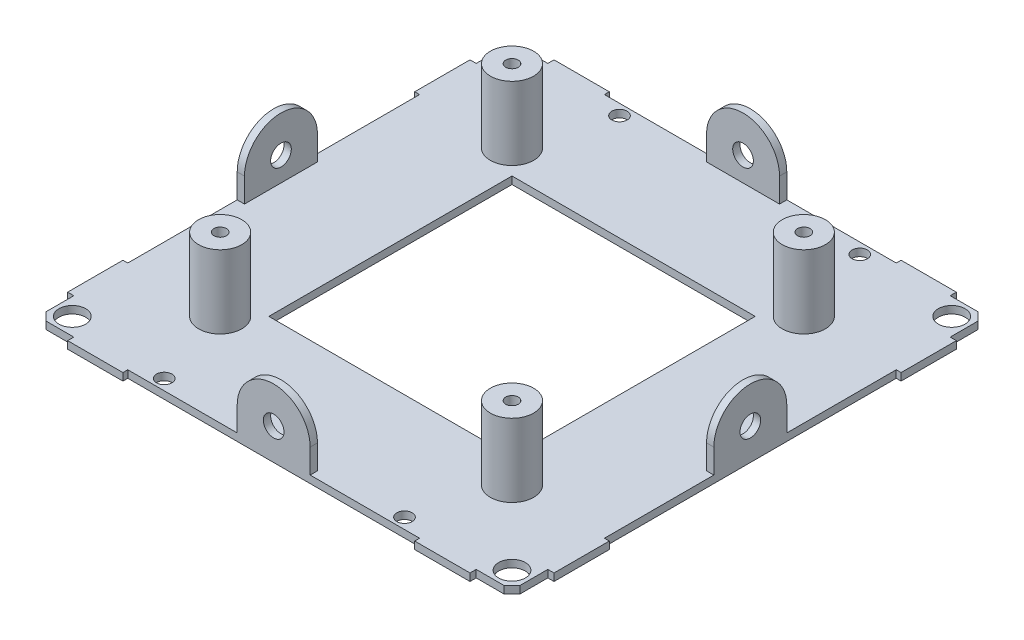
SolidWorks part; units mm, degrees
material "5052-H38"
ref_plane "Front Plane" through (0, 0, 0) normal (0, 0, 1) x (1, 0, 0)
ref_plane "Top Plane" through (0, 0, 0) normal (0, 1, 0) x (1, 0, 0)
ref_plane "Right Plane" through (0, 0, 0) normal (1, 0, 0) x (0, 0, -1)
sketch "Sketch1" plane through (0, 0, 0) normal (0, 1, 0) x (1, 0, 0)
  line L0 (-50, 50) -> (-41.364, 50)
  line L1 (-50, -50) -> (50, -50)
  line L2 (-50, -50) -> (-50, 50)
  line L3 (-50, 50) -> (50, 50)
  line L4 (50, -50) -> (50, 50)
  line L5 (-50, -50) -> (50, 50) construction
  line L6 (-50, 50) -> (50, -50) construction
  line L7 (-50, 50) -> (-50, 41.364)
  line L8 (-50, 41.364) -> (-48.73, 41.364)
  line L9 (-48.73, 41.364) -> (-48.73, 47.079)
  line L10 (-41.364, 50) -> (-41.364, 48.73)
  line L11 (-41.364, 48.73) -> (-47.079, 48.73)
  line L12 (-47.079, 48.73) -> (-48.73, 47.079)
  line L13 (-50, 50) -> (-45.2, 50) construction
  line L14 (-45.2, 50) -> (-45.2, 45.2) construction
  line L15 (50, 50) -> (50, 41.364)
  line L16 (50, 41.364) -> (48.73, 41.364)
  line L17 (48.73, 41.364) -> (48.73, 47.079)
  line L18 (48.73, 47.079) -> (47.079, 48.73)
  line L19 (41.364, 48.73) -> (47.079, 48.73)
  line L20 (41.364, 50) -> (41.364, 48.73)
  line L21 (50, 50) -> (41.364, 50)
  line L22 (50, -50) -> (41.364, -50)
  line L23 (41.364, -50) -> (41.364, -48.73)
  line L24 (41.364, -48.73) -> (47.079, -48.73)
  line L25 (47.079, -48.73) -> (48.73, -47.079)
  line L26 (48.73, -41.364) -> (48.73, -47.079)
  line L27 (50, -41.364) -> (48.73, -41.364)
  line L28 (50, -50) -> (50, -41.364)
  line L29 (-50, -50) -> (-50, -41.364)
  line L30 (-50, -41.364) -> (-48.73, -41.364)
  line L31 (-48.73, -41.364) -> (-48.73, -47.079)
  line L32 (-48.73, -47.079) -> (-47.079, -48.73)
  line L33 (-41.364, -48.73) -> (-47.079, -48.73)
  line L34 (-41.364, -50) -> (-41.364, -48.73)
  line L35 (-50, -50) -> (-41.364, -50)
  line L36 (0, -50) -> (0, 50) construction
  line L37 (-1000, 46.8) -> (49000, 46.8) construction
  line L38 (24.7, 46.8) -> (-24.7, 46.8)
  line L39 (-1000, 0) -> (49000, 0) construction
  line L41 (-25, -25) -> (25, -25)
  line L42 (-25, -25) -> (-25, 25)
  line L43 (-25, 25) -> (25, 25)
  line L44 (25, -25) -> (25, 25)
  line L45 (-25, -25) -> (25, 25) construction
  line L46 (-25, 25) -> (25, -25) construction
  circle A0 centre (-45.2, 45.2) radius 2.7503
  circle A1 centre (45.2, 45.2) radius 2.7503
  circle A2 centre (45.2, -45.2) radius 2.7503
  circle A3 centre (-45.2, -45.2) radius 2.7503
  circle A4 centre (-24.7, 46.8) radius 1.575
  circle A5 centre (24.7, 46.8) radius 1.575
  circle A6 centre (24.7, -46.8) radius 1.575
  circle A7 centre (-24.7, -46.8) radius 1.575
  point P0 (0, 0)
  point P15 (0, 46.8)
  point P45 (0, 0)
  point P46 (0, 0)
  point P48 (-24.7, 46.8)
  point P53 (0, 46.8)
  point P61 (25, 25)
  point P63 (0, 0)
  dimension "D4" = 4
  dimension "D1" = 100
  dimension "D2" = 100
  dimension "D3" = 8.636
  dimension "D5" = 3.2
  dimension "D6" = 24.7
extrude "Boss-Extrude1" add sketch "Sketch1" along normal blind 1.524 contours L37 A5 L38 A4 A0 L9 L8 L2 L30 L31 L32 L33 L34 L1 L23 L24 L25 L26 L27 L4 L16 L17 A1 A2 A3 A6 A7
sketch "Sketch2" plane through (0, 1.524, 0) normal (0, 1, 0) x (1, 0, 0)
  line L0 (0, -1000) -> (0, 49000) construction
  line L1 (0, 50) -> (0, 45) construction
  line L2 (-41.364, 50) -> (41.364, 50) construction
  line L3 (-7.5, 47.5) -> (7.5, 47.5) construction
  line L4 (-7.5, 47.5) -> (7.5, 47.5)
  line L5 (-7.5, 47.5) -> (-7.5, 50)
  line L6 (7.5, 47.5) -> (7.5, 50)
  line L7 (-7.5, 50) -> (7.5, 50)
  line L8 (47.5, 7.5) -> (47.5, -7.5)
  line L9 (47.5, 7.5) -> (50, 7.5)
  line L10 (50, 7.5) -> (50, -7.5)
  line L11 (47.5, -7.5) -> (50, -7.5)
  line L12 (7.5, -47.5) -> (-7.5, -47.5)
  line L13 (7.5, -47.5) -> (7.5, -50)
  line L14 (7.5, -50) -> (-7.5, -50)
  line L15 (-7.5, -47.5) -> (-7.5, -50)
  line L16 (-47.5, -7.5) -> (-47.5, 7.5)
  line L17 (-47.5, -7.5) -> (-50, -7.5)
  line L18 (-50, -7.5) -> (-50, 7.5)
  line L19 (-47.5, 7.5) -> (-50, 7.5)
  point P10 (0, 47.5)
  point P27 (0, 0)
  dimension "D1" = 15
  dimension "D2" = 4
extrude "Boss-Extrude2" add sketch "Sketch2" along normal blind 12.476 contours L4 L5 L7 L6 | L8 L11 L10 L9 | L12 L15 L14 L13 | L16 L19 L18 L17
sketch "Sketch3" plane through (0, 0, 50) normal (0, 0, 1) x (1, 0, 0)
  line L0 (-1007.5, 1.524) -> (48992.5, 1.524) construction
  line L1 (7.5, 1.524) -> (-7.5, 1.524) construction
  line L2 (-7.5, 14) -> (-7.5, 1.524) construction
  line L3 (0, 1.524) -> (0, 6.5) construction
  line L4 (7.5, 14) -> (7.5, 1.524) construction
  line L5 (7.5, 6.5) -> (7.5, 14)
  line L6 (7.5, 14) -> (-7.5, 14)
  line L7 (-7.5, 14) -> (-7.5, 6.5)
  circle A0 centre (0, 6.5) radius 2.125
  arc A1 (-7.5, 6.5) -> (7.5, 6.5) centre (0, 6.5) cw
  line M4 (7.5, 1.524) -> (7.5, 14)
  line M5 (7.5, 14) -> (-7.5, 14)
  line M6 (-7.5, 14) -> (-7.5, 1.524)
extrude "Cut-Extrude1" cut sketch "Sketch3" against normal through all both and the other way through all contours A1 M5 M4 | A1 L6 M6 | A0
sketch "Sketch4" plane through (-50, 0, 0) normal (-1, 0, 0) x (0, 0, 1)
  line L0 (-992.5, 1.524) -> (49007.5, 1.524) construction
  line L1 (-7.5, 1.524) -> (7.5, 1.524) construction
  line L2 (41.364, 1.524) -> (7.5, 1.524) construction
  line L3 (0, 1.524) -> (0, 6.5) construction
  line L4 (7.5, 14) -> (7.5, 1.524) construction
  line L5 (-7.5, 14) -> (-7.5, 1.524) construction
  line L6 (7.5, 6.5) -> (7.5, 14)
  line L7 (7.5, 14) -> (-7.5, 14)
  line L8 (-7.5, 14) -> (-7.5, 6.5)
  circle A0 centre (0, 6.5) radius 2.125
  arc A1 (7.5, 6.5) -> (-7.5, 6.5) centre (0, 6.5) ccw
  line M4 (7.5, 1.524) -> (7.5, 14)
  line M5 (7.5, 14) -> (-7.5, 14)
  line M6 (-7.5, 14) -> (-7.5, 1.524)
extrude "Cut-Extrude2" cut sketch "Sketch4" against normal through all both and the other way through all contours A0 | A1 M4 M5 | A1 L7 M6
sketch "Sketch5" plane through (0, 0, 0) normal (0, -1, 0) x (1, 0, 0)
  line L0 (-1000, -50) -> (49000, -50) construction
  line L1 (-7.5, -50) -> (7.5, -50) construction
  line L2 (0, -1000) -> (0, 49000) construction
  line L3 (-30, -50) -> (30, -50) construction
  line L4 (-30, -50) -> (-30, -49) construction
  line L5 (-50, 30) -> (-49, 30) construction
  line L6 (-30, -49) -> (30, -49)
  line L7 (-30, -49) -> (-30, -50)
  line L8 (-30, -50) -> (30, -50)
  line L9 (30, -49) -> (30, -50)
  line L10 (-49, 30) -> (-50, 30)
  line L11 (-49, 30) -> (-49, -30)
  line L12 (-49, -30) -> (-50, -30)
  line L13 (-50, 30) -> (-50, -30)
  line L14 (30, 50) -> (30, 49) construction
  line L15 (30, 49) -> (30, 50)
  line L16 (30, 49) -> (-30, 49)
  line L17 (-30, 49) -> (-30, 50)
  line L18 (30, 50) -> (-30, 50)
  line L19 (50, -30) -> (49, -30) construction
  line L20 (49, -30) -> (50, -30)
  line L21 (49, -30) -> (49, 30)
  line L22 (49, 30) -> (50, 30)
  line L23 (50, -30) -> (50, 30)
  point P5 (0, -50)
  point P11 (0, -50)
  point P28 (0, 0)
  dimension "D1" = 4
extrude "Cut-Extrude3" cut sketch "Sketch5" against normal through all both and the other way through all
sketch "Sketch6" plane through (0, 1.524, 0) normal (0, 1, 0) x (1, 0, 0)
  circle A0 centre (30, 30) radius 4.445
  circle A1 centre (30, -30) radius 4.445
  circle A2 centre (-30, -30) radius 4.445
  circle A3 centre (-30, 30) radius 4.445
  point P0 (30, 30)
  point P12 (0, 0)
  dimension "D1" = 4
extrude "Boss-Extrude3" add sketch "Sketch6" along normal blind 15
hole_wizard "#5-40 Tapped Hole1" positions "Sketch7" profile "Sketch8" tap size "#5-40" standard "ANSI Inch"
sketch "Sketch7" plane through (0, 16.524, 0) normal (0, 1, 0) x (1, 0, 0)
  point P0 (-17.223, 16.8349)
  point P2 (-17.223, 16.8349)
  point P5 (-30, 30)
  point P8 (-30, -30)
  point P11 (30, -30)
  point P14 (30, 30)
sketch "Sketch8" plane through (-17.223, 16.524, -16.8349) normal (1, 0, 0) x (0, 0, 1)
  line L0 (0, 0) -> (0, 15.7745)
  line L1 (0, 15.7745) -> (1.289, 15)
  line L2 (1.289, 15) -> (1.289, 0)
  line L5 (1.289, 0) -> (0, 0)
  line L10 (0, 15.7745) -> (-1.2891, 15) construction
  line L11 (0, -6.35) -> (0, 107.95) construction
  dimension "Tap Drill Dia." = 2.5781
  dimension "Tap Drill Depth" = 15
  dimension "Drill Angle" = 118
cosmetic thread "Hole Thread1" parameters "D1"=15, "D2"=3.175
cosmetic thread "Hole Thread2" parameters "D1"=15, "D2"=3.175
cosmetic thread "Hole Thread3" parameters "D1"=15, "D2"=3.175
cosmetic thread "Hole Thread4" parameters "D1"=15, "D2"=3.175
